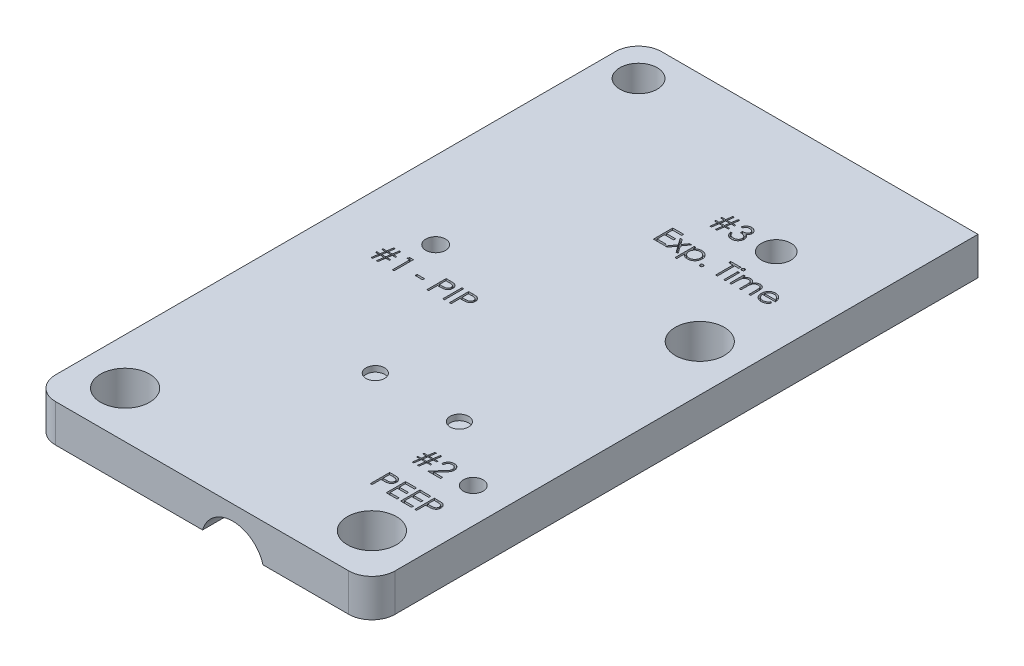
SolidWorks part; units mm, degrees
material "ABS"
ref_plane "Front Plane" through (0, 0, 0) normal (0, 0, 1) x (1, 0, 0)
ref_plane "Top Plane" through (0, 0, 0) normal (0, 1, 0) x (1, 0, 0)
ref_plane "Right Plane" through (0, 0, 0) normal (1, 0, 0) x (0, 0, -1)
sketch "Sketch1" plane through (0, 0, 0) normal (0, 1, 0) x (1, 0, 0)
  line L12 (-23.25, 38.325) -> (-23.25, -38.325)
  line L13 (23.25, 41.5) -> (-20.075, 41.5)
  line L14 (23.25, -38.325) -> (23.25, 41.5)
  line L15 (-20.075, -41.5) -> (20.075, -41.5)
  line L16 (-23.25, 38.325) -> (-23.25, -38.325)
  line L17 (23.25, 41.5) -> (-20.075, 41.5)
  line L18 (23.25, -38.325) -> (23.25, 41.5)
  line L19 (-20.075, -41.5) -> (20.075, -41.5)
  circle A2 centre (-18.4748, 36.7375) radius 2.5591
  arc A9 (-20.075, 41.5) -> (-23.25, 38.325) centre (-20.075, 38.325) ccw
  arc A10 (20.075, -41.5) -> (23.25, -38.325) centre (20.075, -38.325) ccw
  arc A11 (-23.25, -38.325) -> (-20.075, -41.5) centre (-20.075, -38.325) ccw
  arc A12 (-20.075, 41.5) -> (-23.25, 38.325) centre (-20.075, 38.325) ccw
  arc A13 (20.075, -41.5) -> (23.25, -38.325) centre (20.075, -38.325) ccw
  arc A14 (-23.25, -38.325) -> (-20.075, -41.5) centre (-20.075, -38.325) ccw
  circle A28 centre (-18.4748, 36.7375) radius 2.5591
  circle A30 centre (16.9, 9.75) radius 3.3528
  circle A31 centre (16.9, 9.75) radius 3.3528
  circle A33 centre (16.9, -35.15) radius 3.3528
  circle A34 centre (16.9, -35.15) radius 3.3528
  circle A36 centre (-16.9, -35.15) radius 3.3528
  circle A37 centre (-16.9, -35.15) radius 3.3528
  dimension "D1" = 0
  dimension "D2" = 0.1778
  dimension "D3" = 0.1778
  dimension "D4" = 0.1778
  dimension "D5" = 0.1778
extrude "Boss-Extrude1" add sketch "Sketch1" along normal up to surface (5.1594 mm away)
sketch "Sketch2" plane through (0, 5.1594, 0) normal (0, 1, 0) x (1, 0, 0)
  line L0 (8.2492, 25.625) -> (14.7411, 25.625) construction
  line L5 (10.1388, 34.515) -> (4.2, 6.575) construction
  line L6 (16.6307, 34.515) -> (5.9263, -15.845) construction
  line L7 (23.25, 41.5) -> (-20.075, 41.5) construction
  circle A0 centre (11.4951, 25.625) radius 2.0193
  circle A1 centre (-12.65, 3.1337) radius 1.3526
  circle A2 centre (18.4748, -22.8475) radius 1.3525
  arc A5 (-12.265, 1.8371) -> (-12.265, 4.4303) centre (-12.65, 3.1337) ccw construction
  arc A6 (18.8598, -24.1441) -> (18.8598, -21.5509) centre (18.4748, -22.8475) ccw construction
  point P20 (12.2053, 28.9661)
  dimension "D1" = 4.0386
  dimension "D3" = 2.7051
  dimension "D4" = 2.7051
  dimension "D2" = 15.875
extrude "Cut-Extrude1" cut sketch "Sketch2" against normal through all
sketch "Sketch3" plane through (0, 0, -41.5) normal (0, 0, -1) x (-1, 0, 0)
  circle A0 centre (-13.725, -1.1906) radius 4.3053
  circle A1 centre (6.56, -1.1906) radius 4.3053
  arc A2 (2.4226, 0) -> (10.6974, 0) centre (6.56, -1.1906) ccw construction
  arc A3 (-17.8624, 0) -> (-9.5876, 0) centre (-13.725, -1.1906) ccw construction
extrude "Cut-Extrude2" cut sketch "Sketch3" against normal up to surface (6.985 mm away)
sketch "Sketch4" plane through (0, 0, 41.5) normal (0, 0, 1) x (1, 0, 0)
  circle A0 centre (4.2, -1.1906) radius 4.3053
  arc A1 (0.0626, 0) -> (8.3374, 0) centre (4.2, -1.1906) ccw construction
  arc A2 (0.0626, 0) -> (8.3374, 0) centre (4.2, -1.1906) ccw construction
  point P6 (3.4532, -3.0979)
extrude "Cut-Extrude3" cut sketch "Sketch4" against normal up to surface (7.62 mm away)
sketch "Sketch5" plane through (0, 5.1594, 0) normal (0, 1, 0) x (1, 0, 0)
  line L0 (-1.5547, -16.615) -> (-1.5547, -15.845) construction
  line L1 (3.2078, -16.615) -> (-6.65, -16.615) construction
  line L2 (2.4737, -15.845) -> (-6.65, -15.845) construction
  line L3 (9.9547, -15.845) -> (9.9547, -16.615) construction
  line L4 (14.4748, -15.845) -> (5.9263, -15.845) construction
  line L5 (14.4748, -16.615) -> (5.1922, -16.615) construction
  line L6 (9.9547, -16.615) -> (5.1922, -16.615) construction
  line L7 (3.2078, -16.615) -> (-1.5547, -16.615) construction
  circle A0 centre (-1.5547, -16.23) radius 1.27
  circle A1 centre (9.9547, -16.23) radius 1.27
  dimension "D2" = 2.54
  dimension "D1" = 4.7625
extrude "Cut-Extrude4" cut sketch "Sketch5" against normal blind 0.7874
sketch "Sketch6" plane through (0, 5.1594, 0) normal (0, 1, 0) x (1, 0, 0)
  text T0 "#1 - PIP" font "Century Gothic" height in points 10
  text T1 "#2\r\nPEEP" font "Century Gothic" height in points 10
  text T2 "  #3 \r\nExp. Time" font "Century Gothic" height in points 10
  point P3 (0, 0)
  point P4 (0, 0)
  point P5 (0, 0)
extrude "Cut-Extrude5" cut sketch "Sketch6" against normal blind 0.508
